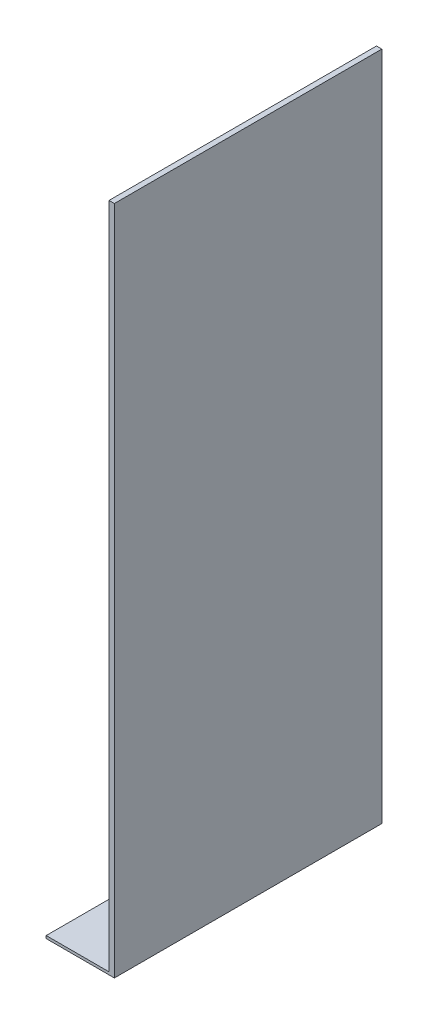
SolidWorks part; units mm, degrees
ref_plane "Front Plane" through (0, 0, 0) normal (0, 0, 1) x (1, 0, 0)
ref_plane "Top Plane" through (0, 0, 0) normal (0, 1, 0) x (1, 0, 0)
ref_plane "Right Plane" through (0, 0, 0) normal (1, 0, 0) x (0, 0, -1)
sketch "Sketch1" plane through (0, 0, 0) normal (1, 0, 0) x (0, 0, -1)
  line L1 (-138.7209, 103.7791) -> (61.2791, 103.7791)
  line L2 (-138.7209, 103.7791) -> (-138.7209, -397.8209)
  line L3 (-138.7209, -397.8209) -> (61.2791, -397.8209)
  line L4 (61.2791, 103.7791) -> (61.2791, -397.8209)
  dimension "D1" = 200
  dimension "D2" = 501.6
extrude "Boss-Extrude1" add sketch "Sketch1" along normal blind 4
sketch "Sketch2" plane through (0, 0, 0) normal (-1, 0, 0) x (0, 0, 1)
  line L0 (138.7209, 103.7791) -> (138.7209, -397.8209) construction
  line L1 (-61.2791, -397.8209) -> (138.7209, -397.8209)
  line L2 (-61.2791, -397.8209) -> (-61.2791, -395.8209)
  line L3 (-61.2791, -395.8209) -> (138.7209, -395.8209)
  line L4 (138.7209, -397.8209) -> (138.7209, -395.8209)
  dimension "D1" = 2
extrude "Boss-Extrude2" add sketch "Sketch2" along normal blind 47
